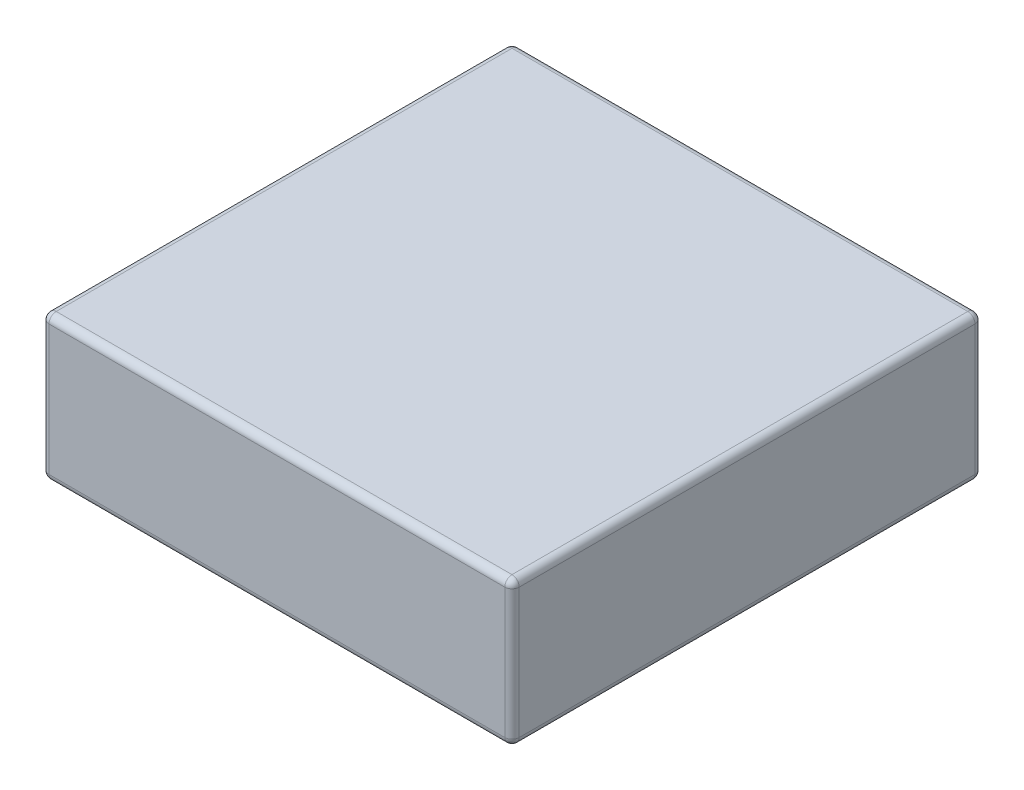
SolidWorks part; units mm, degrees
ref_plane "Front Plane" through (0, 0, 0) normal (0, 0, 1) x (1, 0, 0)
ref_plane "Top Plane" through (0, 0, 0) normal (0, 1, 0) x (1, 0, 0)
ref_plane "Right Plane" through (0, 0, 0) normal (1, 0, 0) x (0, 0, -1)
sketch "Sketch1" plane through (0, 0, 0) normal (0, 1, 0) x (1, 0, 0)
  line L1 (0, 0) -> (65, 0)
  line L2 (0, 0) -> (0, 65)
  line L3 (0, 65) -> (65, 65)
  line L4 (65, 0) -> (65, 65)
  dimension "D1" = 65
  dimension "D2" = 65
extrude "Boss-Extrude1" add sketch "Sketch1" along normal blind 20
fillet "Fillet1" radius 1 12 edges at (0, 10, 0) (65, 10, 0) (65, 10, -65) (0, 10, -65) (32.5, 20, -65) (65, 20, -32.5) (32.5, 20, 0) (0, 20, -32.5) (32.5, 0, 0) (65, 0, -32.5) (32.5, 0, -65) (0, 0, -32.5)
sketch "Sketch5" plane through (0, 20, 0) normal (0, 1, 0) x (1, 0, 0)
  line L0 (1, 64) -> (64, 1) construction
  text T0 "lens filters" font "Arial Narrow" height in points 28
extrude "Boss-Extrude2" add sketch "Sketch5" against normal offset from surface (2 mm away) 2 up to face at (32.5, 20, -32.5)
